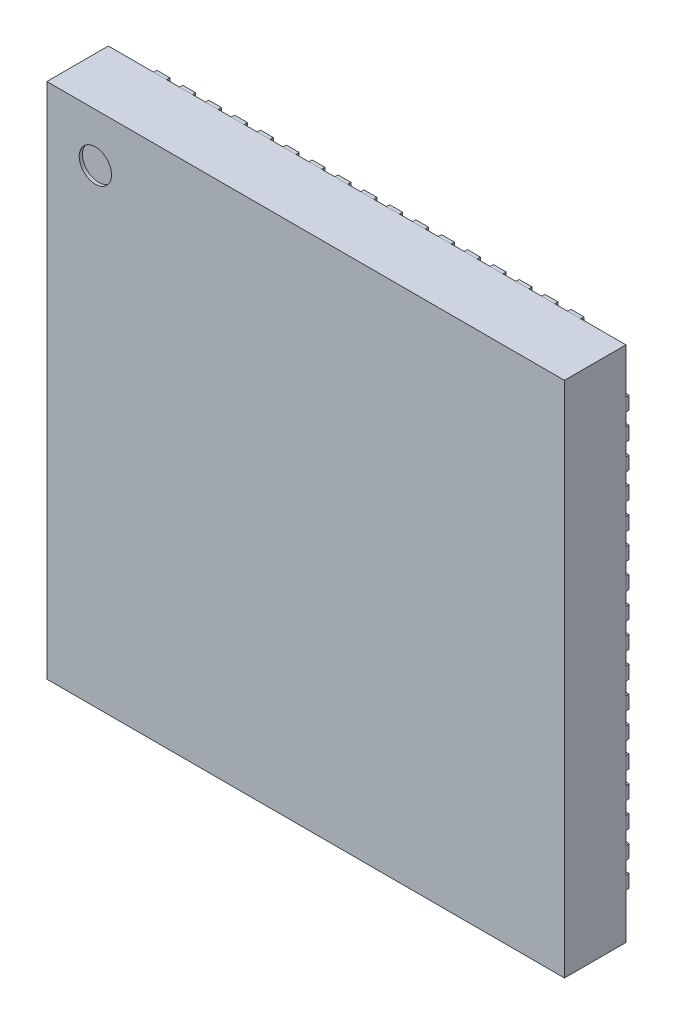
SolidWorks part; units mm, degrees
ref_plane "Front Plane" through (0, 0, 0) normal (0, 0, 1) x (1, 0, 0)
ref_plane "Top Plane" through (0, 0, 0) normal (0, 1, 0) x (1, 0, 0)
ref_plane "Right Plane" through (0, 0, 0) normal (1, 0, 0) x (0, 0, -1)
sketch "Sketch1" plane through (0, 0, 0) normal (0, 0, 1) x (1, 0, 0)
  line L1 (0, 0) -> (8, 0)
  line L2 (0, 0) -> (0, 8)
  line L3 (0, 8) -> (8, 8)
  line L4 (8, 0) -> (8, 8)
  dimension "D1" = 8
  dimension "D2" = 8
extrude "Boss-Extrude1" add sketch "Sketch1" along normal blind 0.95
sketch "Sketch2" plane through (0, 0, 0) normal (0, 0, -1) x (-1, 0, 0)
  line L0 (-4, 8) -> (-4, 0) construction
  line L1 (-8, 8) -> (0, 8) construction
  line L2 (0, 0) -> (-8, 0) construction
  line L3 (-3.7, 8) -> (-3.5, 8)
  line L4 (-8, 0) -> (-8, 8) construction
  line L5 (-8, 4) -> (0, 4) construction
  line L6 (0, 8) -> (0, 0) construction
  line L7 (-4.1, 8) -> (-3.9, 8)
  line L8 (-4.1, 8) -> (-4.1, 7.61)
  line L9 (-3.7, 8) -> (-3.7, 7.61)
  line L10 (-3.9, 8) -> (-3.9, 7.61)
  line L11 (-3.5, 8) -> (-3.5, 7.61)
  line L12 (-3.3, 8) -> (-3.1, 8)
  line L13 (-3.3, 8) -> (-3.3, 7.61)
  line L14 (-3.1, 8) -> (-3.1, 7.61)
  line L15 (-2.9, 8) -> (-2.7, 8)
  line L16 (-2.9, 8) -> (-2.9, 7.61)
  line L17 (-2.7, 8) -> (-2.7, 7.61)
  line L18 (-2.5, 8) -> (-2.3, 8)
  line L19 (-2.5, 8) -> (-2.5, 7.61)
  line L20 (-2.3, 8) -> (-2.3, 7.61)
  line L21 (-2.1, 8) -> (-1.9, 8)
  line L22 (-2.1, 8) -> (-2.1, 7.61)
  line L23 (-1.9, 8) -> (-1.9, 7.61)
  line L24 (-1.7, 8) -> (-1.5, 8)
  line L25 (-4.5, 8) -> (-4.3, 8)
  line L26 (-4.5, 8) -> (-4.5, 7.61)
  line L27 (-4.3, 8) -> (-4.3, 7.61)
  line L28 (-4.9, 8) -> (-4.7, 8)
  line L29 (-4.9, 8) -> (-4.9, 7.61)
  line L30 (-4.7, 8) -> (-4.7, 7.61)
  line L31 (-5.3, 8) -> (-5.1, 8)
  line L32 (-5.3, 8) -> (-5.3, 7.61)
  line L33 (-5.1, 8) -> (-5.1, 7.61)
  line L34 (-5.7, 8) -> (-5.5, 8)
  line L35 (-5.7, 8) -> (-5.7, 7.61)
  line L36 (-5.5, 8) -> (-5.5, 7.61)
  line L37 (-6.1, 8) -> (-5.9, 8)
  line L38 (-6.1, 8) -> (-6.1, 7.61)
  line L39 (-5.9, 8) -> (-5.9, 7.61)
  line L40 (-6.5, 8) -> (-6.3, 8)
  line L41 (-6.5, 8) -> (-6.5, 7.61)
  line L42 (-6.3, 8) -> (-6.3, 7.61)
  line L43 (-6.9, 8) -> (-6.7, 8)
  line L44 (-6.9, 8) -> (-6.9, 7.61)
  line L45 (-6.7, 8) -> (-6.7, 7.61)
  line L46 (-7.3, 8) -> (-7.1, 8)
  line L47 (-7.3, 8) -> (-7.3, 7.61)
  line L48 (-7.1, 8) -> (-7.1, 7.61)
  line L49 (-1.7, 8) -> (-1.7, 7.61)
  line L50 (-1.5, 8) -> (-1.5, 7.61)
  line L51 (-1.3, 8) -> (-1.1, 8)
  line L52 (-1.3, 8) -> (-1.3, 7.61)
  line L53 (-1.1, 8) -> (-1.1, 7.61)
  line L54 (-0.9, 8) -> (-0.7, 8)
  line L55 (-0.9, 8) -> (-0.9, 7.61)
  line L56 (-0.7, 8) -> (-0.7, 7.61)
  line L57 (0, 3.7) -> (0, 3.5)
  line L58 (0, 4.1) -> (0, 3.9)
  line L59 (0, 4.1) -> (-0.39, 4.1)
  line L60 (0, 3.7) -> (-0.39, 3.7)
  line L61 (0, 3.9) -> (-0.39, 3.9)
  line L62 (0, 3.5) -> (-0.39, 3.5)
  line L63 (0, 3.3) -> (0, 3.1)
  line L64 (0, 3.3) -> (-0.39, 3.3)
  line L65 (0, 3.1) -> (-0.39, 3.1)
  line L66 (0, 2.9) -> (0, 2.7)
  line L67 (0, 2.9) -> (-0.39, 2.9)
  line L68 (0, 2.7) -> (-0.39, 2.7)
  line L69 (0, 2.5) -> (0, 2.3)
  line L70 (0, 2.5) -> (-0.39, 2.5)
  line L71 (0, 2.3) -> (-0.39, 2.3)
  line L72 (0, 2.1) -> (0, 1.9)
  line L73 (0, 2.1) -> (-0.39, 2.1)
  line L74 (0, 1.9) -> (-0.39, 1.9)
  line L75 (0, 1.7) -> (0, 1.5)
  line L76 (0, 4.5) -> (0, 4.3)
  line L77 (0, 4.5) -> (-0.39, 4.5)
  line L78 (0, 4.3) -> (-0.39, 4.3)
  line L79 (0, 4.9) -> (0, 4.7)
  line L80 (0, 4.9) -> (-0.39, 4.9)
  line L81 (0, 4.7) -> (-0.39, 4.7)
  line L82 (0, 5.3) -> (0, 5.1)
  line L83 (0, 5.3) -> (-0.39, 5.3)
  line L84 (0, 5.1) -> (-0.39, 5.1)
  line L85 (0, 5.7) -> (0, 5.5)
  line L86 (0, 5.7) -> (-0.39, 5.7)
  line L87 (0, 5.5) -> (-0.39, 5.5)
  line L88 (0, 6.1) -> (0, 5.9)
  line L89 (0, 6.1) -> (-0.39, 6.1)
  line L90 (0, 5.9) -> (-0.39, 5.9)
  line L91 (0, 6.5) -> (0, 6.3)
  line L92 (0, 6.5) -> (-0.39, 6.5)
  line L93 (0, 6.3) -> (-0.39, 6.3)
  line L94 (0, 6.9) -> (0, 6.7)
  line L95 (0, 6.9) -> (-0.39, 6.9)
  line L96 (0, 6.7) -> (-0.39, 6.7)
  line L97 (0, 7.3) -> (0, 7.1)
  line L98 (0, 7.3) -> (-0.39, 7.3)
  line L99 (0, 7.1) -> (-0.39, 7.1)
  line L100 (0, 1.7) -> (-0.39, 1.7)
  line L101 (0, 1.5) -> (-0.39, 1.5)
  line L102 (0, 1.3) -> (0, 1.1)
  line L103 (0, 1.3) -> (-0.39, 1.3)
  line L104 (0, 1.1) -> (-0.39, 1.1)
  line L105 (0, 0.9) -> (0, 0.7)
  line L106 (0, 0.9) -> (-0.39, 0.9)
  line L107 (0, 0.7) -> (-0.39, 0.7)
  line L108 (-4.3, 0) -> (-4.5, 0)
  line L109 (-3.9, 0) -> (-4.1, 0)
  line L110 (-3.9, 0) -> (-3.9, 0.39)
  line L111 (-4.3, 0) -> (-4.3, 0.39)
  line L112 (-4.1, 0) -> (-4.1, 0.39)
  line L113 (-4.5, 0) -> (-4.5, 0.39)
  line L114 (-4.7, 0) -> (-4.9, 0)
  line L115 (-4.7, 0) -> (-4.7, 0.39)
  line L116 (-4.9, 0) -> (-4.9, 0.39)
  line L117 (-5.1, 0) -> (-5.3, 0)
  line L118 (-5.1, 0) -> (-5.1, 0.39)
  line L119 (-5.3, 0) -> (-5.3, 0.39)
  line L120 (-5.5, 0) -> (-5.7, 0)
  line L121 (-5.5, 0) -> (-5.5, 0.39)
  line L122 (-5.7, 0) -> (-5.7, 0.39)
  line L123 (-5.9, 0) -> (-6.1, 0)
  line L124 (-5.9, 0) -> (-5.9, 0.39)
  line L125 (-6.1, 0) -> (-6.1, 0.39)
  line L126 (-6.3, 0) -> (-6.5, 0)
  line L127 (-3.5, 0) -> (-3.7, 0)
  line L128 (-3.5, 0) -> (-3.5, 0.39)
  line L129 (-3.7, 0) -> (-3.7, 0.39)
  line L130 (-3.1, 0) -> (-3.3, 0)
  line L131 (-3.1, 0) -> (-3.1, 0.39)
  line L132 (-3.3, 0) -> (-3.3, 0.39)
  line L133 (-2.7, 0) -> (-2.9, 0)
  line L134 (-2.7, 0) -> (-2.7, 0.39)
  line L135 (-2.9, 0) -> (-2.9, 0.39)
  line L136 (-2.3, 0) -> (-2.5, 0)
  line L137 (-2.3, 0) -> (-2.3, 0.39)
  line L138 (-2.5, 0) -> (-2.5, 0.39)
  line L139 (-1.9, 0) -> (-2.1, 0)
  line L140 (-1.9, 0) -> (-1.9, 0.39)
  line L141 (-2.1, 0) -> (-2.1, 0.39)
  line L142 (-1.5, 0) -> (-1.7, 0)
  line L143 (-1.5, 0) -> (-1.5, 0.39)
  line L144 (-1.7, 0) -> (-1.7, 0.39)
  line L145 (-1.1, 0) -> (-1.3, 0)
  line L146 (-1.1, 0) -> (-1.1, 0.39)
  line L147 (-1.3, 0) -> (-1.3, 0.39)
  line L148 (-0.7, 0) -> (-0.9, 0)
  line L149 (-0.7, 0) -> (-0.7, 0.39)
  line L150 (-0.9, 0) -> (-0.9, 0.39)
  line L151 (-6.3, 0) -> (-6.3, 0.39)
  line L152 (-6.5, 0) -> (-6.5, 0.39)
  line L153 (-6.7, 0) -> (-6.9, 0)
  line L154 (-6.7, 0) -> (-6.7, 0.39)
  line L155 (-6.9, 0) -> (-6.9, 0.39)
  line L156 (-7.1, 0) -> (-7.3, 0)
  line L157 (-7.1, 0) -> (-7.1, 0.39)
  line L158 (-7.3, 0) -> (-7.3, 0.39)
  line L159 (-8, 4.3) -> (-8, 4.5)
  line L160 (-8, 3.9) -> (-8, 4.1)
  line L161 (-8, 3.9) -> (-7.61, 3.9)
  line L162 (-8, 4.3) -> (-7.61, 4.3)
  line L163 (-8, 4.1) -> (-7.61, 4.1)
  line L164 (-8, 4.5) -> (-7.61, 4.5)
  line L165 (-8, 4.7) -> (-8, 4.9)
  line L166 (-8, 4.7) -> (-7.61, 4.7)
  line L167 (-8, 4.9) -> (-7.61, 4.9)
  line L168 (-8, 5.1) -> (-8, 5.3)
  line L169 (-8, 5.1) -> (-7.61, 5.1)
  line L170 (-8, 5.3) -> (-7.61, 5.3)
  line L171 (-8, 5.5) -> (-8, 5.7)
  line L172 (-8, 5.5) -> (-7.61, 5.5)
  line L173 (-8, 5.7) -> (-7.61, 5.7)
  line L174 (-8, 5.9) -> (-8, 6.1)
  line L175 (-8, 5.9) -> (-7.61, 5.9)
  line L176 (-8, 6.1) -> (-7.61, 6.1)
  line L177 (-8, 6.3) -> (-8, 6.5)
  line L178 (-1.15, 5.7) -> (-1.15, 1.15)
  line L179 (-6.85, 6.85) -> (-1.15, 6.85)
  line L180 (-6.85, 6.85) -> (-6.85, 1.15)
  line L181 (-6.85, 1.15) -> (-1.15, 1.15)
  line L182 (-1.15, 6.85) -> (-1.15, 6.3)
  line L183 (-8, 3.5) -> (-8, 3.7)
  line L184 (-8, 3.5) -> (-7.61, 3.5)
  line L185 (-8, 3.7) -> (-7.61, 3.7)
  line L186 (-8, 3.1) -> (-8, 3.3)
  line L187 (-8, 3.1) -> (-7.61, 3.1)
  line L188 (-8, 3.3) -> (-7.61, 3.3)
  line L189 (-8, 2.7) -> (-8, 2.9)
  line L190 (-8, 2.7) -> (-7.61, 2.7)
  line L191 (-8, 2.9) -> (-7.61, 2.9)
  line L192 (-8, 2.3) -> (-8, 2.5)
  line L193 (-8, 2.3) -> (-7.61, 2.3)
  line L194 (-8, 2.5) -> (-7.61, 2.5)
  line L195 (-8, 1.9) -> (-8, 2.1)
  line L196 (-8, 1.9) -> (-7.61, 1.9)
  line L197 (-8, 2.1) -> (-7.61, 2.1)
  line L198 (-8, 1.5) -> (-8, 1.7)
  line L199 (-8, 1.5) -> (-7.61, 1.5)
  line L200 (-8, 1.7) -> (-7.61, 1.7)
  line L201 (-8, 1.1) -> (-8, 1.3)
  line L202 (-8, 1.1) -> (-7.61, 1.1)
  line L203 (-8, 1.3) -> (-7.61, 1.3)
  line L204 (-8, 0.7) -> (-8, 0.9)
  line L205 (-8, 0.7) -> (-7.61, 0.7)
  line L206 (-8, 0.9) -> (-7.61, 0.9)
  line L207 (-8, 6.3) -> (-7.61, 6.3)
  line L208 (-8, 6.5) -> (-7.61, 6.5)
  line L209 (-8, 6.7) -> (-8, 6.9)
  line L210 (-8, 6.7) -> (-7.61, 6.7)
  line L211 (-8, 6.9) -> (-7.61, 6.9)
  line L212 (-8, 7.1) -> (-8, 7.3)
  line L213 (-8, 7.1) -> (-7.61, 7.1)
  line L214 (-8, 7.3) -> (-7.61, 7.3)
  arc A0 (-4.1, 7.61) -> (-3.9, 7.61) centre (-4, 7.61) ccw
  arc A1 (-3.7, 7.61) -> (-3.5, 7.61) centre (-3.6, 7.61) ccw
  arc A2 (-3.3, 7.61) -> (-3.1, 7.61) centre (-3.2, 7.61) ccw
  arc A3 (-2.9, 7.61) -> (-2.7, 7.61) centre (-2.8, 7.61) ccw
  arc A4 (-2.5, 7.61) -> (-2.3, 7.61) centre (-2.4, 7.61) ccw
  arc A5 (-2.1, 7.61) -> (-1.9, 7.61) centre (-2, 7.61) ccw
  arc A6 (-1.7, 7.61) -> (-1.5, 7.61) centre (-1.6, 7.61) ccw
  arc A7 (-1.3, 7.61) -> (-1.1, 7.61) centre (-1.2, 7.61) ccw
  arc A8 (-0.9, 7.61) -> (-0.7, 7.61) centre (-0.8, 7.61) ccw
  arc A9 (-4.5, 7.61) -> (-4.3, 7.61) centre (-4.4, 7.61) ccw
  arc A10 (-4.9, 7.61) -> (-4.7, 7.61) centre (-4.8, 7.61) ccw
  arc A11 (-5.3, 7.61) -> (-5.1, 7.61) centre (-5.2, 7.61) ccw
  arc A12 (-5.7, 7.61) -> (-5.5, 7.61) centre (-5.6, 7.61) ccw
  arc A13 (-6.1, 7.61) -> (-5.9, 7.61) centre (-6, 7.61) ccw
  arc A14 (-6.5, 7.61) -> (-6.3, 7.61) centre (-6.4, 7.61) ccw
  arc A15 (-6.9, 7.61) -> (-6.7, 7.61) centre (-6.8, 7.61) ccw
  arc A16 (-7.3, 7.61) -> (-7.1, 7.61) centre (-7.2, 7.61) ccw
  arc A17 (-0.39, 4.1) -> (-0.39, 3.9) centre (-0.39, 4) ccw
  arc A18 (-0.39, 3.7) -> (-0.39, 3.5) centre (-0.39, 3.6) ccw
  arc A19 (-0.39, 3.3) -> (-0.39, 3.1) centre (-0.39, 3.2) ccw
  arc A20 (-0.39, 2.9) -> (-0.39, 2.7) centre (-0.39, 2.8) ccw
  arc A21 (-0.39, 2.5) -> (-0.39, 2.3) centre (-0.39, 2.4) ccw
  arc A22 (-0.39, 2.1) -> (-0.39, 1.9) centre (-0.39, 2) ccw
  arc A23 (-0.39, 1.7) -> (-0.39, 1.5) centre (-0.39, 1.6) ccw
  arc A24 (-0.39, 1.3) -> (-0.39, 1.1) centre (-0.39, 1.2) ccw
  arc A25 (-0.39, 0.9) -> (-0.39, 0.7) centre (-0.39, 0.8) ccw
  arc A26 (-0.39, 4.5) -> (-0.39, 4.3) centre (-0.39, 4.4) ccw
  arc A27 (-0.39, 4.9) -> (-0.39, 4.7) centre (-0.39, 4.8) ccw
  arc A28 (-0.39, 5.3) -> (-0.39, 5.1) centre (-0.39, 5.2) ccw
  arc A29 (-0.39, 5.7) -> (-0.39, 5.5) centre (-0.39, 5.6) ccw
  arc A30 (-0.39, 6.1) -> (-0.39, 5.9) centre (-0.39, 6) ccw
  arc A31 (-0.39, 6.5) -> (-0.39, 6.3) centre (-0.39, 6.4) ccw
  arc A32 (-0.39, 6.9) -> (-0.39, 6.7) centre (-0.39, 6.8) ccw
  arc A33 (-0.39, 7.3) -> (-0.39, 7.1) centre (-0.39, 7.2) ccw
  arc A34 (-3.9, 0.39) -> (-4.1, 0.39) centre (-4, 0.39) ccw
  arc A35 (-4.3, 0.39) -> (-4.5, 0.39) centre (-4.4, 0.39) ccw
  arc A36 (-4.7, 0.39) -> (-4.9, 0.39) centre (-4.8, 0.39) ccw
  arc A37 (-5.1, 0.39) -> (-5.3, 0.39) centre (-5.2, 0.39) ccw
  arc A38 (-5.5, 0.39) -> (-5.7, 0.39) centre (-5.6, 0.39) ccw
  arc A39 (-5.9, 0.39) -> (-6.1, 0.39) centre (-6, 0.39) ccw
  arc A40 (-6.3, 0.39) -> (-6.5, 0.39) centre (-6.4, 0.39) ccw
  arc A41 (-6.7, 0.39) -> (-6.9, 0.39) centre (-6.8, 0.39) ccw
  arc A42 (-7.1, 0.39) -> (-7.3, 0.39) centre (-7.2, 0.39) ccw
  arc A43 (-3.5, 0.39) -> (-3.7, 0.39) centre (-3.6, 0.39) ccw
  arc A44 (-3.1, 0.39) -> (-3.3, 0.39) centre (-3.2, 0.39) ccw
  arc A45 (-2.7, 0.39) -> (-2.9, 0.39) centre (-2.8, 0.39) ccw
  arc A46 (-2.3, 0.39) -> (-2.5, 0.39) centre (-2.4, 0.39) ccw
  arc A47 (-1.9, 0.39) -> (-2.1, 0.39) centre (-2, 0.39) ccw
  arc A48 (-1.5, 0.39) -> (-1.7, 0.39) centre (-1.6, 0.39) ccw
  arc A49 (-1.1, 0.39) -> (-1.3, 0.39) centre (-1.2, 0.39) ccw
  arc A50 (-0.7, 0.39) -> (-0.9, 0.39) centre (-0.8, 0.39) ccw
  arc A51 (-7.61, 3.9) -> (-7.61, 4.1) centre (-7.61, 4) ccw
  arc A52 (-7.61, 4.3) -> (-7.61, 4.5) centre (-7.61, 4.4) ccw
  arc A53 (-7.61, 4.7) -> (-7.61, 4.9) centre (-7.61, 4.8) ccw
  arc A54 (-7.61, 5.1) -> (-7.61, 5.3) centre (-7.61, 5.2) ccw
  arc A55 (-7.61, 5.5) -> (-7.61, 5.7) centre (-7.61, 5.6) ccw
  arc A56 (-7.61, 5.9) -> (-7.61, 6.1) centre (-7.61, 6) ccw
  arc A57 (-7.61, 6.3) -> (-7.61, 6.5) centre (-7.61, 6.4) ccw
  arc A58 (-7.61, 6.7) -> (-7.61, 6.9) centre (-7.61, 6.8) ccw
  arc A59 (-7.61, 7.1) -> (-7.61, 7.3) centre (-7.61, 7.2) ccw
  arc A60 (-7.61, 3.5) -> (-7.61, 3.7) centre (-7.61, 3.6) ccw
  arc A61 (-7.61, 3.1) -> (-7.61, 3.3) centre (-7.61, 3.2) ccw
  arc A62 (-7.61, 2.7) -> (-7.61, 2.9) centre (-7.61, 2.8) ccw
  arc A63 (-7.61, 2.3) -> (-7.61, 2.5) centre (-7.61, 2.4) ccw
  arc A64 (-7.61, 1.9) -> (-7.61, 2.1) centre (-7.61, 2) ccw
  arc A65 (-7.61, 1.5) -> (-7.61, 1.7) centre (-7.61, 1.6) ccw
  arc A66 (-7.61, 1.1) -> (-7.61, 1.3) centre (-7.61, 1.2) ccw
  arc A67 (-7.61, 0.7) -> (-7.61, 0.9) centre (-7.61, 0.8) ccw
  arc A68 (-1.15, 5.7) -> (-1.15, 6.3) centre (-1.15, 6) cw
  point P16 (-4, 8)
  point P18 (-4, 4)
  point P356 (-4, 4)
  point P359 (-4, 6.85)
  point P360 (-6.85, 4)
  point P367 (-4, 4)
  dimension "D7" = 0.3
  dimension "D1" = 0.2
  dimension "D2" = 0.39
  dimension "D6" = 5.7
  dimension "D8" = 2
  dimension "D4" = 9
  dimension "D3" = 9
extrude "Boss-Extrude2" add sketch "Sketch2" along normal blind 0.05 separate body
sketch "Sketch3" plane through (0, 0, 0.95) normal (0, 0, 1) x (1, 0, 0)
  line L0 (0, 8) -> (0, 0) construction
  line L1 (8, 8) -> (0, 8) construction
  circle A0 centre (0.75, 7.25) radius 0.25
  dimension "D1" = 0.5
  dimension "D2" = 0.75
  dimension "D3" = 0.75
extrude "Cut-Extrude1" cut sketch "Sketch3" against normal blind 0.05
